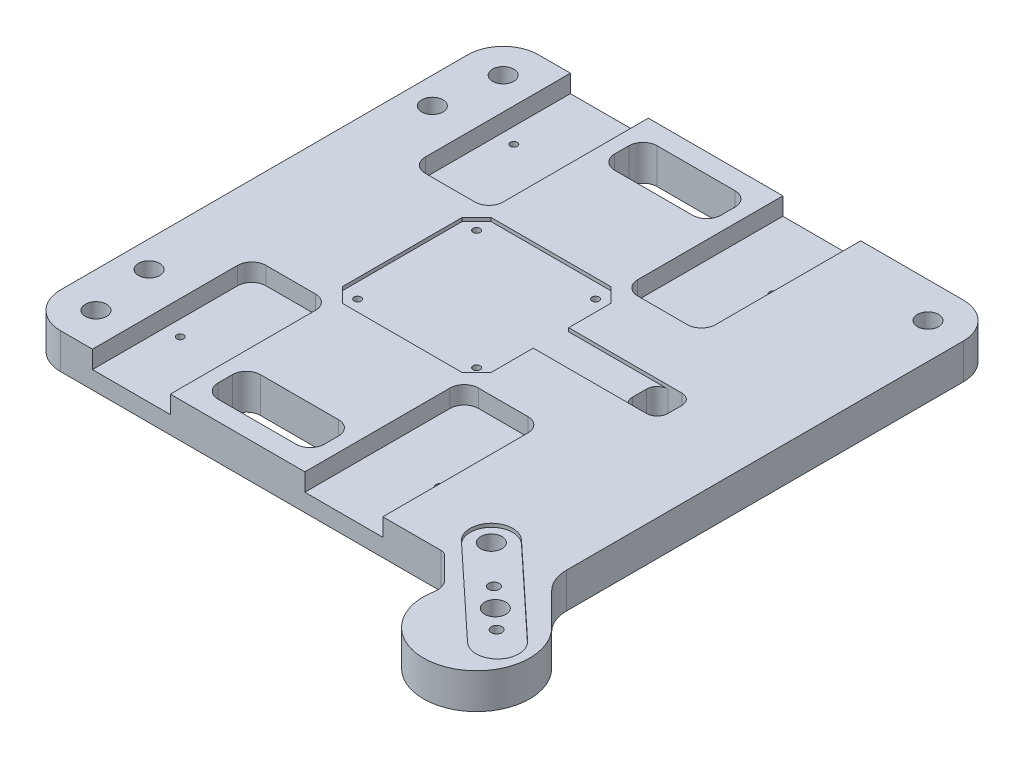
SolidWorks part; units mm, degrees
material "Plastique personnalisé"
ref_plane "Plan de face" through (0, 0, 0) normal (0, 0, 1) x (1, 0, 0)
ref_plane "Plan de dessus" through (0, 0, 0) normal (0, 1, 0) x (1, 0, 0)
ref_plane "Plan de droite" through (0, 0, 0) normal (1, 0, 0) x (0, 0, -1)
sketch "Esquisse2" plane through (0, 0, 0) normal (0, 1, 0) x (1, 0, 0)
  line L2 (0, -9.3395) -> (0, 9.3395) construction
  line L3 (0, 75) -> (0, -75) construction
  line L4 (59.2337, -68.2322) -> (65.1801, -74.1786)
  line L5 (80, 57.5) -> (80, -54.6447)
  line L6 (-50, 67.5) -> (70, 67.5)
  line L9 (-50, -67.5) -> (57.466, -67.5)
  line L10 (-60, 57.5) -> (-60, -57.5)
  line L11 (82.9289, -61.7157) -> (91.9239, -70.7107)
  line L12 (-185.7212, 0) -> (165.7799, 0) construction
  line L15 (0, 0) -> (81.3173, -81.3173) construction
  arc A0 (-50, 67.5) -> (-60, 57.5) centre (-50, 57.5) ccw
  arc A1 (-60, -57.5) -> (-50, -67.5) centre (-50, -57.5) ccw
  arc A2 (70, 67.5) -> (80, 57.5) centre (70, 57.5) cw
  circle A3 centre (-52.5, 40) radius 3
  arc A8 (82.9289, -61.7157) -> (80, -54.6447) centre (90, -54.6447) cw
  arc A9 (91.9239, -70.7107) -> (66.5627, -78.6149) centre (81.3173, -81.3173) cw
  arc A11 (65.1801, -74.1786) -> (66.5627, -78.6149) centre (61.6445, -77.7141) cw
  arc A20 (57.466, -67.5) -> (59.2337, -68.2322) centre (57.466, -70) cw
  circle A37 centre (-52.5, -40) radius 3
  point P33 (-60, 67.5)
  point P37 (-60, -67.5)
  point P56 (58.5015, -67.5)
  dimension "D3" = 67.5
  dimension "D7" = 10
  dimension "D10" = 67.5
  dimension "D11" = 2.5
  dimension "D8" = 15
  dimension "D17" = 80
  dimension "D6" = 10
  dimension "D15" = 5
  dimension "D4" = 10
  dimension "D22" = 27.5
  dimension "D23" = 6
  dimension "D5" = 60
  dimension "D12" = 115
  dimension "D19" = 7.5
extrude "Boss.-Extru.1" add sketch "Esquisse2" along normal blind 10
hole_wizard "board holes" positions "Esquisse4" profile "Esquisse5" hole size "Ø2.0" standard "ISO" end condition up to next
sketch "Esquisse4" plane through (0, 10, 0) normal (0, 1, 0) x (1, 0, 0)
  line L0 (-36.6, 47.1) -> (36.6, 47.1) construction
  line L1 (36.6, 47.1) -> (36.6, -47.1) construction
  line L2 (36.6, -47.1) -> (-36.6, -47.1) construction
  line L4 (-36.6, 47.1) -> (-36.6, -47.1) construction
  point P0 (-36.6, 47.1)
  point P2 (36.6, 47.1)
  point P4 (36.6, -47.1)
  point P6 (-36.6, -47.1)
  dimension "D1" = 73.2
  dimension "D2" = 94.2
  dimension "D3" = 36.6
  dimension "D4" = 47.1
sketch "Esquisse5" plane through (-36.6, 10, -47.1) normal (1, 0, 0) x (0, 0, 1)
  line L0 (0, 0) -> (0, 10)
  line L1 (0, 10) -> (1, 10)
  line L2 (1, 10) -> (1, 0)
  line L5 (1, 0) -> (0, 0)
  line L11 (0, -6.35) -> (0, 107.95) construction
  dimension "Diamètre du perçage jusqu'au prochain" = 2
  dimension "Profondeur du perçage jusqu'au prochain" = 10
hole_wizard "stepper holes" positions "Esquisse6" profile "Esquisse7" hole size "Ø2.0" standard "Ansi Metric" end condition up to next
sketch "Esquisse6" plane through (0, 10, 0) normal (0, 1, 0) x (1, 0, 0)
  line L0 (-16.8, 16.8) -> (16.8, 16.8) construction
  line L1 (16.8, 16.8) -> (16.8, -16.8) construction
  line L2 (16.8, -16.8) -> (-16.8, -16.8) construction
  line L3 (-16.8, -16.8) -> (-16.8, 16.8) construction
  point P0 (-16.8, 16.8)
  point P2 (16.8, 16.8)
  point P4 (16.8, -16.8)
  point P6 (-16.8, -16.8)
  dimension "D1" = 33.6
  dimension "D2" = 33.6
  dimension "D3" = 16.8
  dimension "D4" = 16.8
sketch "Esquisse7" plane through (-16.8, 10, -16.8) normal (1, 0, 0) x (0, 0, 1)
  line L0 (0, 0) -> (0, 10)
  line L1 (0, 10) -> (1, 10)
  line L2 (1, 10) -> (1, 0)
  line L5 (1, 0) -> (0, 0)
  line L11 (0, -6.35) -> (0, 107.95) construction
  dimension "Diamètre du perçage jusqu'au prochain" = 2
  dimension "Profondeur du perçage jusqu'au prochain" = 10
hole_wizard "feet holes" positions "Esquisse8" profile "Esquisse9" hole size "Ø6.0" standard "Ansi Metric" end condition up to next
sketch "Esquisse8" plane through (0, 10, 0) normal (0, 1, 0) x (1, 0, 0)
  line L0 (-50, 57.5) -> (-50, -57.5) construction
  line L3 (0, 0) -> (78.2548, -72.9738) construction
  line L6 (-50, -57.5) -> (61.6612, -57.5) construction
  arc A7 (-60, -57.5) -> (-50, -67.5) centre (-50, -57.5) ccw construction
  arc A8 (-50, 67.5) -> (-60, 57.5) centre (-50, 57.5) ccw construction
  arc A9 (80, 57.5) -> (70, 67.5) centre (70, 57.5) ccw construction
  point P29 (70, 57.5)
  point P32 (-50, 57.5)
  point P35 (-50, -57.5)
  point P37 (78.2548, -72.9738)
  point P76 (61.6612, -57.5)
  dimension "D1" = 107
  dimension "D2" = 43
sketch "Esquisse9" plane through (70, 10, -57.5) normal (1, 0, 0) x (0, 0, 1)
  line L0 (0, 0) -> (0, 10)
  line L1 (0, 10) -> (3, 10)
  line L2 (3, 10) -> (3, 0)
  line L5 (3, 0) -> (0, 0)
  line L11 (0, -6.35) -> (0, 107.95) construction
  dimension "Diamètre du perçage jusqu'au prochain" = 6
  dimension "Profondeur du perçage jusqu'au prochain" = 10
chamfer "Chanfrein1" distance 1 angle 45 4 edges at (-36.6, 10, -46.1) (-36.6, 10, 48.1) (36.6, 10, 48.1) (36.6, 10, -46.1)
sketch "Esquisse10" plane through (0, 10, -10) normal (0, -1, 0) x (1, 0, 0)
  line L0 (-16.9, 31) -> (16.9, 31)
  line L1 (16.9, 31) -> (21, 26.9)
  line L2 (21, 26.9) -> (21, 15)
  line L3 (21, 10) -> (0, 10) construction
  line L4 (0, 10) -> (0, 31) construction
  line L5 (-21, 26.9) -> (-21, -6.9)
  line L6 (-16.9, 31) -> (-21, 26.9)
  line L7 (-16.9, -11) -> (-21, -6.9)
  line L8 (16.9, -11) -> (21, -6.9)
  line L9 (-16.9, -11) -> (16.9, -11)
  line L10 (21, 15) -> (56, 15)
  line L11 (56, 15) -> (56, 5)
  line L12 (21, -6.9) -> (21, 5)
  line L13 (21, 5) -> (56, 5)
  line L14 (-60, -47.5) -> (-60, 67.5) construction
  point P11 (-21, 10)
  point P13 (16.8, 26.8)
  point P19 (56, 10)
  dimension "D1" = 16.9
  dimension "D2" = 10
  dimension "D3" = 16.9
  dimension "D4" = 21
  dimension "D5" = 4.2
  dimension "D6" = 21
  dimension "D7" = 39
  dimension "D8" = 35
extrude "stepper" cut sketch "Esquisse10" along normal blind 1
sketch "Esquisse11" plane through (0, 10, 0) normal (0, 1, 0) x (1, 0, 0)
  line L0 (-41, -67.5) -> (-19, -67.5)
  line L1 (-50, -67.5) -> (57.466, -67.5) construction
  line L2 (-41, -67.5) -> (-41, -26.5)
  line L3 (-37, -22.5) -> (-23, -22.5)
  line L4 (-19, -67.5) -> (-19, -26.5)
  line L5 (0, 70) -> (0, -70) construction
  line L7 (19, -67.5) -> (19, -26.5)
  line L8 (37, -22.5) -> (23, -22.5)
  line L10 (41, -67.5) -> (41, -26.5)
  line L12 (0, 0) -> (92.4984, 0) construction
  line L13 (41, -67.5) -> (19, -67.5)
  line L15 (41, 67.5) -> (19, 67.5)
  line L17 (41, 67.5) -> (41, 26.5)
  line L18 (37, 22.5) -> (23, 22.5)
  line L19 (19, 67.5) -> (19, 26.5)
  line L20 (-19, 67.5) -> (-19, 26.5)
  line L21 (-37, 22.5) -> (-23, 22.5)
  line L22 (-41, 67.5) -> (-41, 26.5)
  line L24 (-41, 67.5) -> (-19, 67.5)
  arc A0 (-23, -22.5) -> (-19, -26.5) centre (-23, -26.5) cw
  arc A1 (-41, -26.5) -> (-37, -22.5) centre (-37, -26.5) cw
  arc A3 (41, -26.5) -> (37, -22.5) centre (37, -26.5) ccw
  arc A4 (23, -22.5) -> (19, -26.5) centre (23, -26.5) ccw
  arc A5 (23, 22.5) -> (19, 26.5) centre (23, 26.5) cw
  arc A6 (41, 26.5) -> (37, 22.5) centre (37, 26.5) cw
  arc A7 (-41, 26.5) -> (-37, 22.5) centre (-37, 26.5) ccw
  arc A8 (-23, 22.5) -> (-19, 26.5) centre (-23, 26.5) ccw
  point P0 (15, -75)
  dimension "D1" = 4
  dimension "D2" = 45
  dimension "D3" = 41
  dimension "D4" = 22
extrude "pumps" cut sketch "Esquisse11" against normal blind 5
sketch "Esquisse13" plane through (0, 10, 0) normal (0, 1, 0) x (1, 0, 0)
  line L0 (39.8202, 0) -> (-32.3605, 0) construction
  line L1 (11, 62) -> (-11, 62)
  line L2 (15, 58) -> (15, 54)
  line L3 (11, 50) -> (-11, 50)
  line L4 (-15, 58) -> (-15, 54)
  line L5 (-15, -58) -> (-15, -54)
  line L6 (11, -50) -> (-11, -50)
  line L7 (15, -58) -> (15, -54)
  line L8 (11, -62) -> (-11, -62)
  arc A0 (-11, 62) -> (-15, 58) centre (-11, 58) ccw
  arc A1 (-11, 50) -> (-15, 54) centre (-11, 54) cw
  arc A2 (15, 54) -> (11, 50) centre (11, 54) cw
  arc A3 (11, 62) -> (15, 58) centre (11, 58) cw
  arc A4 (11, -62) -> (15, -58) centre (11, -58) ccw
  arc A5 (15, -54) -> (11, -50) centre (11, -54) ccw
  arc A6 (-11, -50) -> (-15, -54) centre (-11, -54) ccw
  arc A7 (-11, -62) -> (-15, -58) centre (-11, -58) cw
  dimension "D5" = 4
  dimension "D1" = 12
  dimension "D2" = 30
  dimension "D3" = 15
  dimension "D4" = 50
extrude "wires" cut sketch "Esquisse13" against normal through all
sketch "Esquisse14" plane through (0, 10, 0) normal (0, 1, 0) x (1, 0, 0)
  line L0 (0, 0) -> (121.6182, 0) construction
  line L1 (0, 0) -> (92.1285, -85.9112) construction
  line L2 (62.1651, -57.9699) -> (87.7624, -81.8398) construction
  line L3 (66.2571, -53.5817) -> (91.8544, -77.4517)
  line L4 (58.0731, -62.358) -> (83.6705, -86.2279)
  arc A0 (66.2571, -53.5817) -> (58.0731, -62.358) centre (62.1651, -57.9699) ccw
  arc A1 (83.6705, -86.2279) -> (91.8544, -77.4517) centre (87.7624, -81.8398) ccw
  point P4 (74.9638, -69.9048)
  dimension "D1" = 12
  dimension "D2" = 43
  dimension "D3" = 35
  dimension "D4" = 85
extrude "weight" cut sketch "Esquisse14" against normal blind 1
hole_wizard "Weight holes" positions "Esquisse15" profile "Esquisse16" hole size "Ø3.0" standard "Ansi Metric" end condition up to next
sketch "Esquisse15" plane through (0, 9, 0) normal (0, 1, 0) x (1, 0, 0)
  line L6 (83.691, -78.0431) -> (72.7207, -67.8132) construction
  line L8 (0, 0) -> (115.3713, 0) construction
  line L11 (91.8544, -77.4517) -> (66.2571, -53.5817) construction
  point P27 (83.691, -78.0431)
  point P29 (72.7207, -67.8132)
  point P56 (77.5728, -73.7052)
  dimension "D1" = 15
  dimension "D2" = 6
  dimension "D3" = 7.5
sketch "Esquisse16" plane through (83.691, 9, 78.0431) normal (1, 0, 0) x (0, 0, 1)
  line L0 (0, 0) -> (0, 9)
  line L1 (0, 9) -> (1.5, 9)
  line L2 (1.5, 9) -> (1.5, 0)
  line L5 (1.5, 0) -> (0, 0)
  line L11 (0, -6.35) -> (0, 107.95) construction
  dimension "Diamètre du perçage jusqu'au prochain" = 3
  dimension "Profondeur du perçage jusqu'au prochain" = 9
sketch "Esquisse17" plane through (0, 9, 0) normal (0, 1, 0) x (1, 0, 0)
  line L1 (56, -5) -> (46, -5)
  line L2 (56, -5) -> (56, 5)
  line L3 (56, 5) -> (46, 5)
  line L4 (46, -5) -> (46, 5)
  point P7 (0, 0)
  point P8 (34.2098, -2.6362)
  point P11 (0, 0)
  point P13 (0, 0)
  dimension "D1" = 10
extrude "wires stepper" cut sketch "Esquisse17" against normal through all
fillet "Congé1" radius 3 4 edges at (56, 5, -5) (46, 4.5, 5) (46, 4.5, -5) (56, 5, 5)
